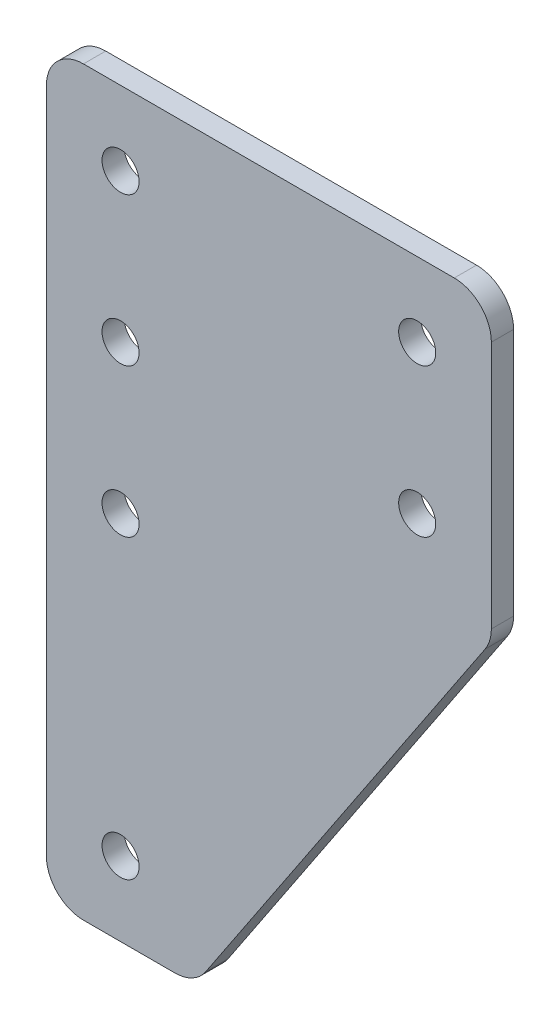
SolidWorks part; units mm, degrees
ref_plane "Front Plane" through (0, 0, 0) normal (0, 0, 1) x (1, 0, 0)
ref_plane "Top Plane" through (0, 0, 0) normal (0, 1, 0) x (1, 0, 0)
ref_plane "Right Plane" through (0, 0, 0) normal (1, 0, 0) x (0, 0, -1)
sketch "Sketch1" plane through (0, 0, 0) normal (0, 0, 1) x (1, 0, 0)
  line L0 (0, 0) -> (20, 0)
  line L1 (20, 0) -> (60, 60)
  line L2 (60, 60) -> (60, 100)
  line L3 (60, 100) -> (0, 100)
  line L4 (0, 100) -> (0, 0)
  dimension "D1" = 20
  dimension "D2" = 40
  dimension "60" = 60
  dimension "D4" = 100
extrude "Boss-Extrude1" add sketch "Sketch1" along normal blind 3
sketch "Sketch3" plane through (0, 0, 3) normal (0, 0, 1) x (1, 0, 0)
  line L0 (60, 100) -> (0, 100) construction
  line L1 (60, 60) -> (60, 100) construction
  circle A0 centre (50, 90) radius 2.5
  dimension "D1" = 10
  dimension "D2" = 5
  dimension "D3" = 10
extrude "Cut-Extrude1" cut sketch "Sketch3" against normal through all
pattern_linear "LPattern1" count 2 spacing 40 along (-1, 0, 0) count 2 spacing 20 along (0, -1, 0) of "Cut-Extrude1"
sketch "Sketch4" plane through (0, 0, 3) normal (0, 0, 1) x (1, 0, 0)
  line L0 (0, 0) -> (20, 0) construction
  line L1 (0, 100) -> (0, 0) construction
  circle A0 centre (10, 10) radius 2.5
  dimension "D1" = 5
  dimension "D2" = 10
  dimension "D3" = 10
extrude "Cut-Extrude2" cut sketch "Sketch4" against normal through all
pattern_linear "LPattern2" count 2 spacing 40 along (0, 1, 0) of "Cut-Extrude2"
fillet "Fillet1" radius 5 5 edges at (0, 0, 1.5) (20, 0, 1.5) (60, 60, 1.5) (60, 100, 1.5) (0, 100, 1.5)
